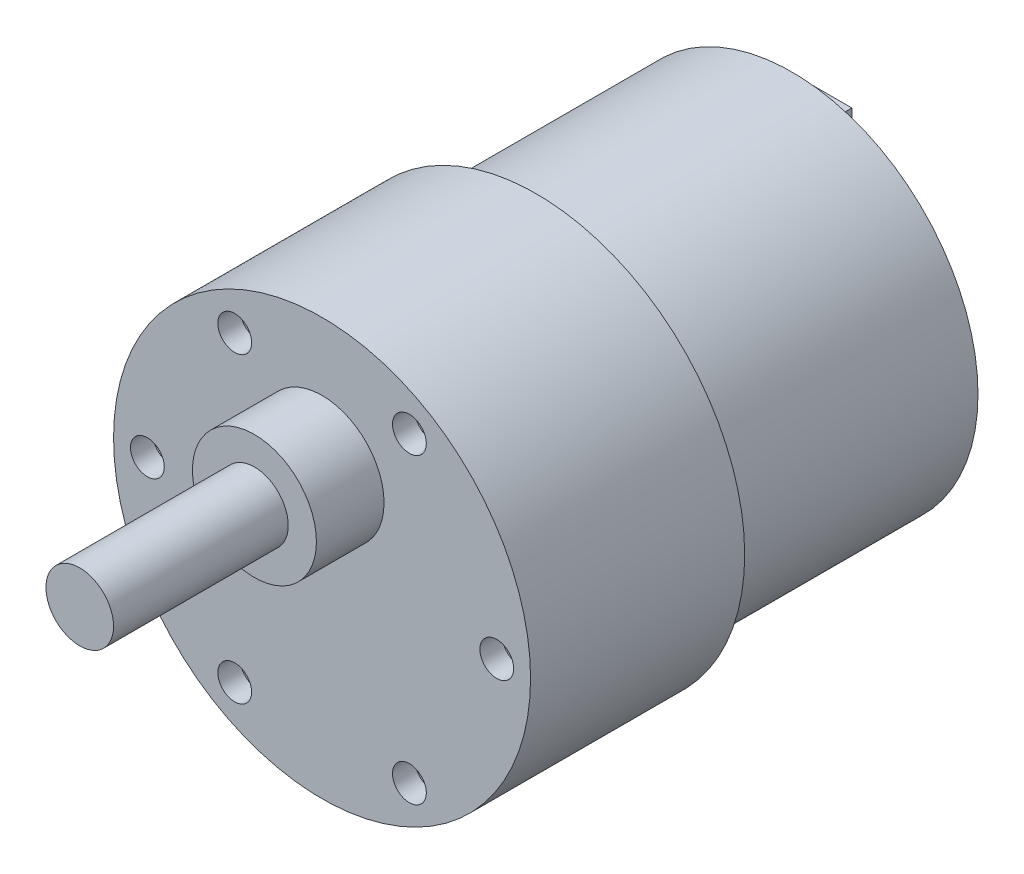
SolidWorks part; units mm, degrees
ref_plane "前视基准面" through (0, 0, 0) normal (0, 0, 1) x (1, 0, 0)
ref_plane "上视基准面" through (0, 0, 0) normal (0, 1, 0) x (1, 0, 0)
ref_plane "右视基准面" through (0, 0, 0) normal (1, 0, 0) x (0, 0, -1)
sketch "草图1" plane through (0, 0, 0) normal (0, 0, 1) x (1, 0, 0)
  line L0 (0, 0) -> (31.8676, 0) construction
  line L1 (0, 0) -> (0, -32.3665) construction
  circle A0 centre (0, 0) radius 16.5
  dimension "D1" = 33
extrude "凸台-拉伸1" add sketch "草图1" along normal blind 22.7
sketch "草图2" plane through (0, 0, 22.7) normal (0, 0, 1) x (1, 0, 0)
  circle A0 centre (0, 0) radius 18.5
  dimension "D1" = 37
extrude "凸台-拉伸2" add sketch "草图2" along normal blind 19
sketch "草图3" plane through (0, 0, 41.7) normal (0, 0, 1) x (1, 0, 0)
  circle A0 centre (0, 0) radius 15.5
  circle A1 centre (15.5, 0) radius 1.5
  circle A2 centre (7.75, -13.4234) radius 1.5
  circle A3 centre (-7.75, -13.4234) radius 1.5
  circle A4 centre (-15.5, 0) radius 1.5
  circle A5 centre (-7.75, 13.4234) radius 1.5
  circle A6 centre (7.75, 13.4234) radius 1.5
  point P17 (0, 0)
  dimension "D1" = 31
  dimension "D2" = 3
  dimension "D3" = 6
extrude "切除-拉伸1" cut sketch "草图3" against normal blind 2 contours A5 | A6 | A4 | A3 | A2 | A1
sketch "草图4" plane through (0, 0, 41.7) normal (0, 0, 1) x (1, 0, 0)
  circle A0 centre (0, 7) radius 5.5
  dimension "D2" = 11
  dimension "D1" = 7
extrude "凸台-拉伸3" add sketch "草图4" along normal blind 6
sketch "草图5" plane through (0, 0, 47.7) normal (0, 0, 1) x (1, 0, 0)
  circle A0 centre (0, 7) radius 3
  dimension "D1" = 6
extrude "凸台-拉伸4" add sketch "草图5" along normal blind 15.5
sketch "草图6" plane through (0, 0, 0) normal (0, 0, -1) x (-1, 0, 0)
  circle A0 centre (0, 0) radius 5
  dimension "D1" = 10
extrude "凸台-拉伸5" add sketch "草图6" along normal blind 2.8
sketch "草图7" plane through (0, 0, 0) normal (0, 0, -1) x (-1, 0, 0)
  line L0 (0, 0) -> (10.5516, 0)
  line L1 (-1.8096, 12.8903) -> (1.8096, 12.8903)
  line L2 (-1.8096, 12.8903) -> (-1.8096, 11.1084)
  line L3 (-1.8096, 11.1084) -> (1.8096, 11.1084)
  line L4 (1.8096, 12.8903) -> (1.8096, 11.1084)
  line L5 (-1.8096, 12.8903) -> (1.8096, 11.1084) construction
  line L6 (-1.8096, 11.1084) -> (1.8096, 12.8903) construction
  line L7 (-1.8096, -11.1084) -> (1.8096, -12.8903) construction
  line L8 (1.8096, -12.8903) -> (1.8096, -11.1084)
  line L9 (-1.8096, -12.8903) -> (1.8096, -12.8903)
  line L10 (-1.8096, -12.8903) -> (1.8096, -11.1084) construction
  line L11 (-1.8096, -11.1084) -> (1.8096, -11.1084)
  line L12 (-1.8096, -12.8903) -> (-1.8096, -11.1084)
  point P0 (0, 11.9994)
  point P12 (0, -11.9994)
extrude "凸台-拉伸6" add sketch "草图7" along normal blind 3.5 contours L4 L1 L2 L3 | L11 L8 L9 L12
